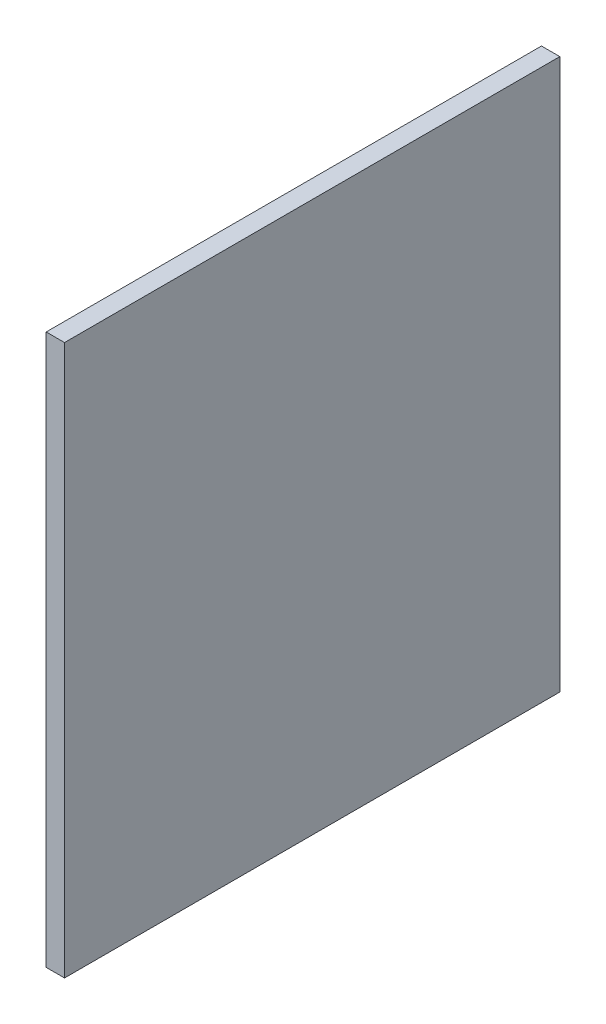
SolidWorks part; units mm, degrees
ref_plane "前视基准面" through (0, 0, 0) normal (0, 0, 1) x (1, 0, 0)
ref_plane "上视基准面" through (0, 0, 0) normal (0, 1, 0) x (1, 0, 0)
ref_plane "右视基准面" through (0, 0, 0) normal (1, 0, 0) x (0, 0, -1)
sketch "草图1" plane through (0, 0, 0) normal (1, 0, 0) x (0, 0, -1)
  line L0 (-44.1285, 33.6868) -> (-44.1285, -266.3132)
  line L1 (-44.1285, -266.3132) -> (205.8715, -266.3132)
  line L2 (205.8715, -266.3132) -> (225.8715, -266.3132)
  line L3 (225.8715, -266.3132) -> (225.8715, 33.6868)
  line L4 (225.8715, 33.6868) -> (-44.1285, 33.6868)
  dimension "D1" = 300
  dimension "D2" = 250
  dimension "D3" = 20
extrude "凸台-拉伸1" add sketch "草图1" along normal blind 10
